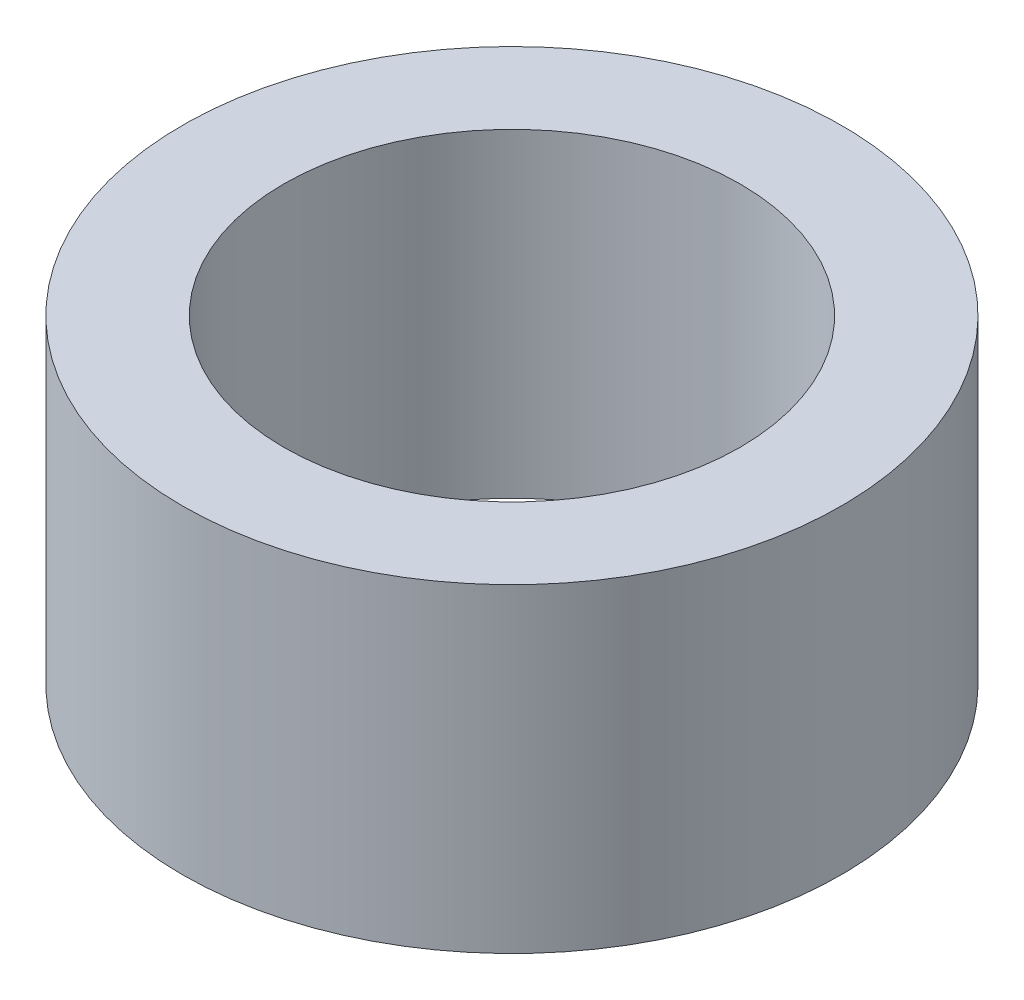
SolidWorks part; units mm, degrees
ref_plane "Front Plane" through (0, 0, 0) normal (0, 0, 1) x (1, 0, 0)
ref_plane "Top Plane" through (0, 0, 0) normal (0, 1, 0) x (1, 0, 0)
ref_plane "Right Plane" through (0, 0, 0) normal (1, 0, 0) x (0, 0, -1)
sketch "Sketch1" plane through (0, 0, 0) normal (0, 1, 0) x (1, 0, 0)
  circle A0 centre (-1.5262, 3.0523) radius 13
  circle A1 centre (-1.5262, 3.0523) radius 9
extrude "Boss-Extrude1" add sketch "Sketch1" along normal blind 12.6
